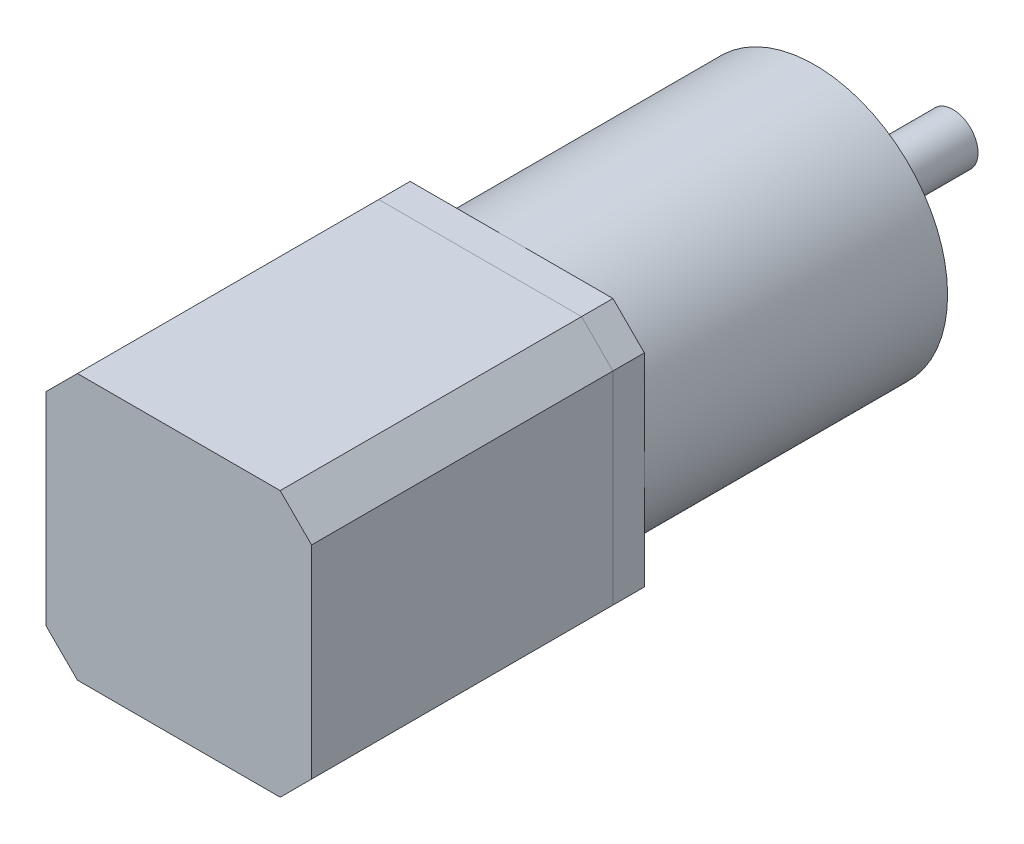
SolidWorks part; units mm, degrees
ref_plane "Front Plane" through (0, 0, 0) normal (0, 0, 1) x (1, 0, 0)
ref_plane "Top Plane" through (0, 0, 0) normal (0, 1, 0) x (1, 0, 0)
ref_plane "Right Plane" through (0, 0, 0) normal (1, 0, 0) x (0, 0, -1)
sketch "Sketch1" plane through (0, 0, 0) normal (0, 0, 1) x (1, 0, 0)
  line L1 (-21.15, 21.15) -> (21.15, 21.15)
  line L2 (-21.15, 21.15) -> (-21.15, -21.15)
  line L3 (-21.15, -21.15) -> (21.15, -21.15)
  line L4 (21.15, 21.15) -> (21.15, -21.15)
  line L5 (-21.15, 21.15) -> (21.15, -21.15) construction
  line L6 (-21.15, -21.15) -> (21.15, 21.15) construction
  point P0 (0, 0)
  dimension "D1" = 42.3
  dimension "D2" = 42.3
extrude "Boss-Extrude1" add sketch "Sketch1" along normal blind 48
chamfer "Chamfer1" distance 5 angle 45 4 edges at (-21.15, -21.15, 24) (21.15, -21.15, 24) (-21.15, 21.15, 24) (21.15, 21.15, 24)
sketch "Sketch2" plane through (0, 0, 0) normal (0, 0, -1) x (-1, 0, 0)
  line L1 (-21.15, -21.15) -> (21.15, -21.15)
  line L2 (-21.15, -21.15) -> (-21.15, 21.15)
  line L3 (-21.15, 21.15) -> (21.15, 21.15)
  line L4 (21.15, -21.15) -> (21.15, 21.15)
  line L5 (-21.15, -21.15) -> (21.15, 21.15) construction
  line L6 (-21.15, 21.15) -> (21.15, -21.15) construction
  point P0 (0, 0)
  dimension "D1" = 42.3
  dimension "D2" = 42.3
extrude "Boss-Extrude2" add sketch "Sketch2" along normal blind 5 separate body
chamfer "Chamfer2" distance 5 angle 45 4 edges at (21.15, -21.15, -2.5) (-21.15, -21.15, -2.5) (21.15, 21.15, -2.5) (-21.15, 21.15, -2.5)
sketch "Sketch3" plane through (0, 0, -5) normal (0, 0, -1) x (-1, 0, 0)
  circle A0 centre (0, 0) radius 21.15
  dimension "D1" = 42.3
extrude "Boss-Extrude3" add sketch "Sketch3" along normal blind 48.3
sketch "Sketch4" plane through (0, 0, -53.3) normal (0, 0, -1) x (-1, 0, 0)
  circle A0 centre (0, 0) radius 11
  dimension "D1" = 22
extrude "Boss-Extrude4" add sketch "Sketch4" along normal blind 2
sketch "Sketch5" plane through (0, 0, -55.3) normal (0, 0, -1) x (-1, 0, 0)
  circle A0 centre (0, 0) radius 4
  dimension "D1" = 8
extrude "Boss-Extrude5" add sketch "Sketch5" along normal blind 20
sketch "Sketch6" plane through (0, 0, -55.3) normal (0, 0, -1) x (-1, 0, 0)
  circle A0 centre (0, 0) radius 6.211
extrude "Boss-Extrude6" add sketch "Sketch6" along normal blind 0.5
sketch "Sketch7" plane through (0, 0, -53.3) normal (0, 0, -1) x (-1, 0, 0)
  circle A0 centre (0, 0) radius 17.5 construction
  circle A1 centre (-17.5, 0) radius 1.5
  circle A2 centre (0, 0) radius 17.5 construction
  circle A3 centre (0, 17.5) radius 1.5
  circle A4 centre (0, 0) radius 17.5 construction
  circle A5 centre (17.5, 0) radius 1.5
  circle A6 centre (0, 0) radius 17.5 construction
  circle A7 centre (0, -17.5) radius 1.5
  point P17 (0, 0)
  dimension "D1" = 35
  dimension "D2" = 3
  dimension "D3" = 4
extrude "Cut-Extrude2" cut sketch "Sketch7" against normal blind 10
